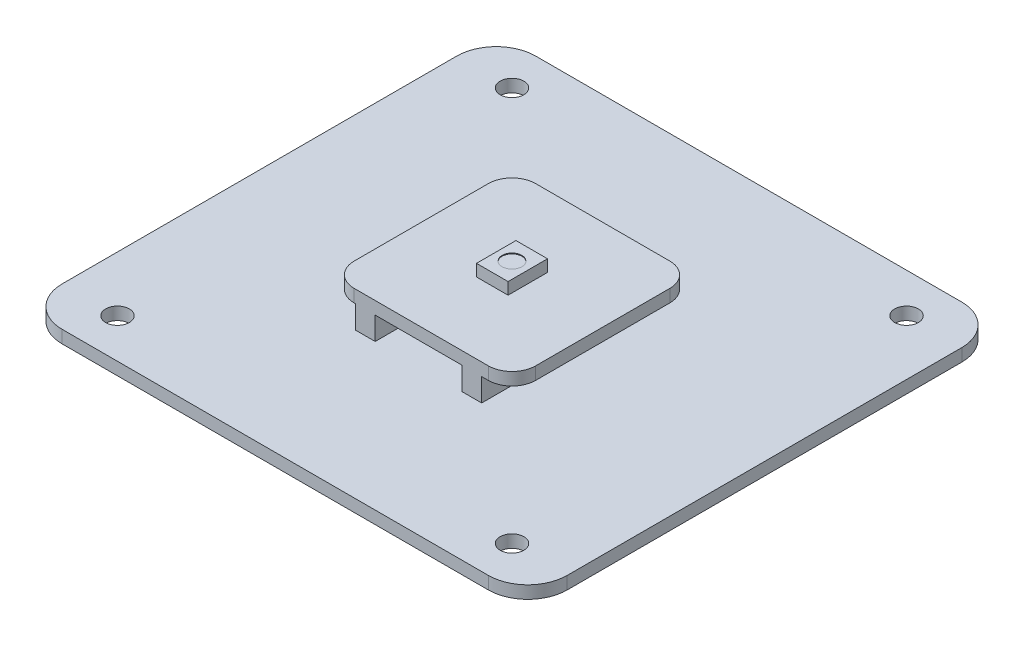
SolidWorks part; units mm, degrees
ref_plane "Front Plane" through (0, 0, 0) normal (0, 0, 1) x (1, 0, 0)
ref_plane "Top Plane" through (0, 0, 0) normal (0, 1, 0) x (1, 0, 0)
ref_plane "Right Plane" through (0, 0, 0) normal (1, 0, 0) x (0, 0, -1)
sketch "Sketch1" plane through (0, 0, 0) normal (0, 1, 0) x (1, 0, 0)
  line L1 (-27, -30) -> (27, -30)
  line L2 (-32, -25) -> (-32, 25)
  line L3 (-27, 30) -> (27, 30)
  line L4 (32, -25) -> (32, 25)
  line L5 (-32, -30) -> (32, 30) construction
  line L6 (-32, 30) -> (32, -30) construction
  circle A0 centre (25, 25) radius 1.5
  circle A1 centre (-25, 25) radius 1.5
  circle A2 centre (-25, -25) radius 1.5
  circle A3 centre (25, -25) radius 1.5
  arc A4 (-27, -30) -> (-32, -25) centre (-27, -25) cw
  arc A5 (27, -30) -> (32, -25) centre (27, -25) ccw
  arc A6 (27, 30) -> (32, 25) centre (27, 25) cw
  arc A7 (-32, 25) -> (-27, 30) centre (-27, 25) cw
  point P0 (0, 0)
  dimension "D3" = 3
  dimension "D4" = 5
  dimension "D5" = 7
  dimension "D8" = 5
  dimension "D1" = 64
  dimension "D2" = 60
  dimension "D6" = 2
  dimension "D7" = 2
extrude "Boss-Extrude1" add sketch "Sketch1" along normal blind 1.6
sketch "Sketch2" plane through (0, 1.6, 0) normal (0, 1, 0) x (1, 0, 0)
  line L1 (-11.5, -11.5) -> (11.5, -11.5)
  line L2 (-11.5, -11.5) -> (-11.5, 11.5)
  line L3 (-11.5, 11.5) -> (11.5, 11.5)
  line L4 (11.5, -11.5) -> (11.5, 11.5)
  line L5 (-11.5, -11.5) -> (11.5, 11.5) construction
  line L6 (-11.5, 11.5) -> (11.5, -11.5) construction
  point P0 (0, 0)
  dimension "D1" = 23
  dimension "D2" = 23
extrude "Boss-Extrude2" add sketch "Sketch2" along normal blind 4.5
sketch "Sketch3" plane through (0, 6.1, 0) normal (0, 1, 0) x (1, 0, 0)
  line L1 (-2, -2.5) -> (2, -2.5)
  line L2 (-2, -2.5) -> (-2, 2.5)
  line L3 (-2, 2.5) -> (2, 2.5)
  line L4 (2, -2.5) -> (2, 2.5)
  line L5 (-2, -2.5) -> (2, 2.5) construction
  line L6 (-2, 2.5) -> (2, -2.5) construction
  point P0 (0, 0)
  dimension "D1" = 5
  dimension "D2" = 4
extrude "Boss-Extrude3" add sketch "Sketch3" along normal blind 1.5
sketch "Sketch4" plane through (0, 0, 11.5) normal (0, 0, 1) x (1, 0, 0)
  line L0 (-11.5, 6.1) -> (-11.5, 1.6) construction
  line L1 (-11.5, 4.5) -> (11.5, 4.5)
  line L2 (-11.5, 4.5) -> (-11.5, 1.6)
  line L3 (-11.5, 1.6) -> (11.5, 1.6)
  line L4 (11.5, 4.5) -> (11.5, 1.6)
  line L5 (-11.5, 6.1) -> (11.5, 6.1) construction
  dimension "D1" = 1.6
extrude "Cut-Extrude3" cut sketch "Sketch4" against normal blind 39.5
sketch "Sketch5" plane through (0, 0, 11.5) normal (0, 0, 1) x (1, 0, 0)
  line L0 (11.5, 4.5) -> (-11.5, 4.5) construction
  line L1 (-8.3404, 4.5) -> (-5.8404, 4.5)
  line L2 (-8.3404, 4.5) -> (-8.3404, 1.6)
  line L3 (-8.3404, 1.6) -> (-5.8404, 1.6)
  line L4 (-5.8404, 4.5) -> (-5.8404, 1.6)
  line L5 (-27, 1.6) -> (27, 1.6) construction
  line L7 (5.1596, 4.5) -> (7.6596, 4.5)
  line L8 (5.1596, 4.5) -> (5.1596, 1.6)
  line L9 (5.1596, 1.6) -> (7.6596, 1.6)
  line L10 (7.6596, 4.5) -> (7.6596, 1.6)
  dimension "D1" = 11
  dimension "D2" = 2.5
  dimension "D3" = 2.5
extrude "Boss-Extrude4" add sketch "Sketch5" against normal up to surface (23 mm away) up to face at (0, 5.3, -11.5)
fillet "Fillet1" radius 3 4 edges at (11.5, 5.3, -11.5) (-11.5, 5.3, -11.5) (-11.5, 5.3, 11.5) (11.5, 5.3, 11.5)
sketch "Sketch6" plane through (0, 7.6, 0) normal (0, 1, 0) x (1, 0, 0)
  circle A0 centre (0, 0) radius 1.25
  dimension "D1" = 2.5
extrude "Cut-Extrude4" cut sketch "Sketch6" against normal blind 0.1
